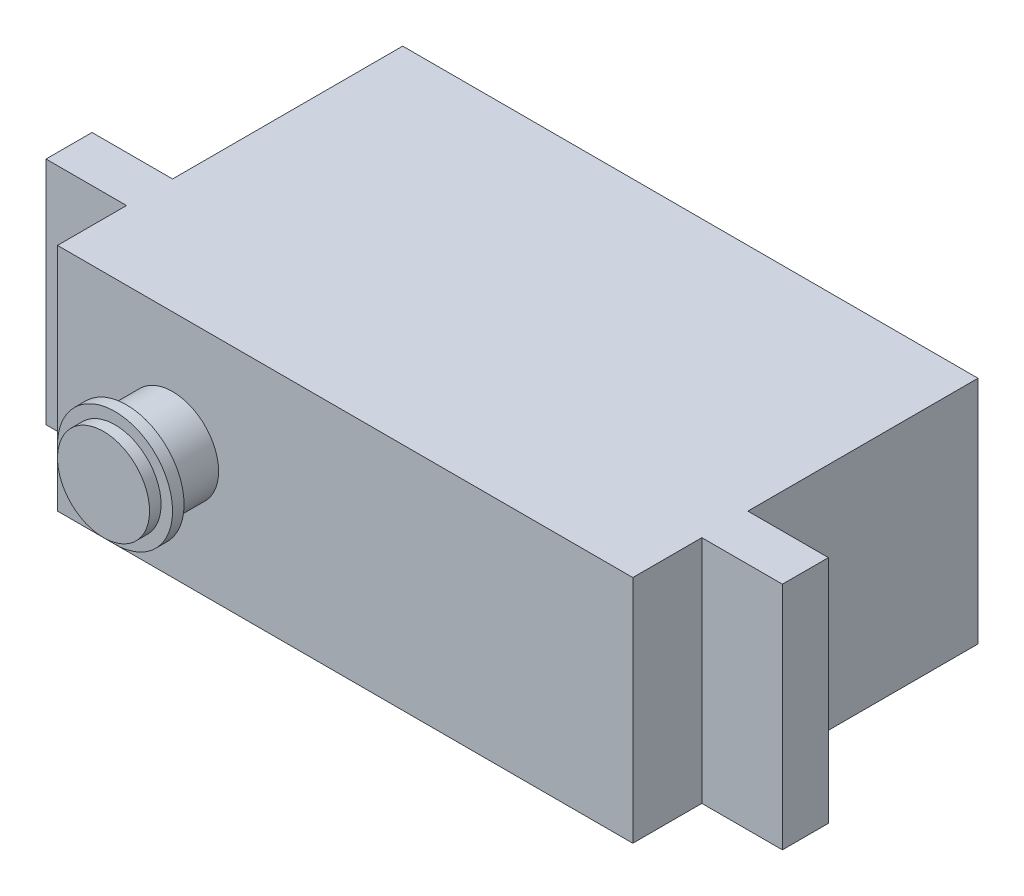
SolidWorks part; units mm, degrees
ref_plane "정면" through (0, 0, 0) normal (0, 0, 1) x (1, 0, 0)
ref_plane "윗면" through (0, 0, 0) normal (0, 1, 0) x (1, 0, 0)
ref_plane "우측면" through (0, 0, 0) normal (1, 0, 0) x (0, 0, -1)
sketch "스케치1" plane through (0, 0, 0) normal (0, 0, 1) x (1, 0, 0)
  line L1 (-12.5, 5) -> (12.5, 5)
  line L2 (-12.5, 5) -> (-12.5, -5)
  line L3 (-12.5, -5) -> (12.5, -5)
  line L4 (12.5, 5) -> (12.5, -5)
  line L5 (-12.5, 5) -> (12.5, -5) construction
  line L6 (-12.5, -5) -> (12.5, 5) construction
  point P0 (0, 0)
  dimension "D1" = 25
  dimension "D2" = 10
extrude "보스-돌출1" add sketch "스케치1" along normal blind 15
ref_plane "평면1" through (0, 0, 15) normal (0, 0, 1) x (1, 0, 0)
sketch "스케치2" plane through (0, 0, 15) normal (0, 0, 1) x (1, 0, 0)
  line L0 (-12.5, 0) -> (12.5, 0) construction
  line L1 (-12.5, 5) -> (-12.5, -5) construction
  line L2 (12.5, -5) -> (12.5, 5) construction
  line L4 (12.5, 5) -> (-12.5, 5) construction
  line L5 (0, 5) -> (0, -5) construction
  line L6 (-12.5, -5) -> (12.5, -5) construction
  circle A0 centre (-7.5, 0) radius 2
  dimension "D2" = 4
  dimension "D1" = 5
extrude "보스-돌출2" add sketch "스케치2" along normal blind 3
ref_plane "평면2" through (12.5, 0, 0) normal (1, 0, 0) x (0, 0, -1)
sketch "스케치3" plane through (12.5, 0, 0) normal (1, 0, 0) x (0, 0, -1)
  line L0 (-15, -5) -> (0, -5) construction
  line L1 (-12, -5) -> (-10, -5)
  line L2 (-12, -5) -> (-12, 5)
  line L3 (-12, 5) -> (-10, 5)
  line L4 (-10, -5) -> (-10, 5)
  line L5 (-15, 5) -> (0, 5) construction
  line L6 (-15, 5.5) -> (-15, -5.5) construction
  dimension "D1" = 3
  dimension "D2" = 2
extrude "보스-돌출3" add sketch "스케치3" along normal blind 3.5
ref_plane "평면3" through (-12.5, 0, 0) normal (-1, 0, 0) x (0, 0, 1)
sketch "스케치4" plane through (-12.5, 0, 0) normal (-1, 0, 0) x (0, 0, 1)
  line L0 (15, 5) -> (0, 5) construction
  line L1 (10, 5) -> (12, 5)
  line L2 (10, 5) -> (10, -5)
  line L3 (10, -5) -> (12, -5)
  line L4 (12, 5) -> (12, -5)
  line L5 (15, -5) -> (0, -5) construction
  line L6 (15, -5.5) -> (15, 5.5) construction
  dimension "D1" = 2
  dimension "D2" = 3
extrude "보스-돌출4" add sketch "스케치4" along normal blind 3.5
sketch "스케치7" plane through (0, 0, 15) normal (0, 0, 1) x (1, 0, 0)
  circle A0 centre (-7.5, 0) radius 2.5
  dimension "D1" = 5
extrude "보스-돌출5" add sketch "스케치7" along normal blind 0.5 from offset 2
